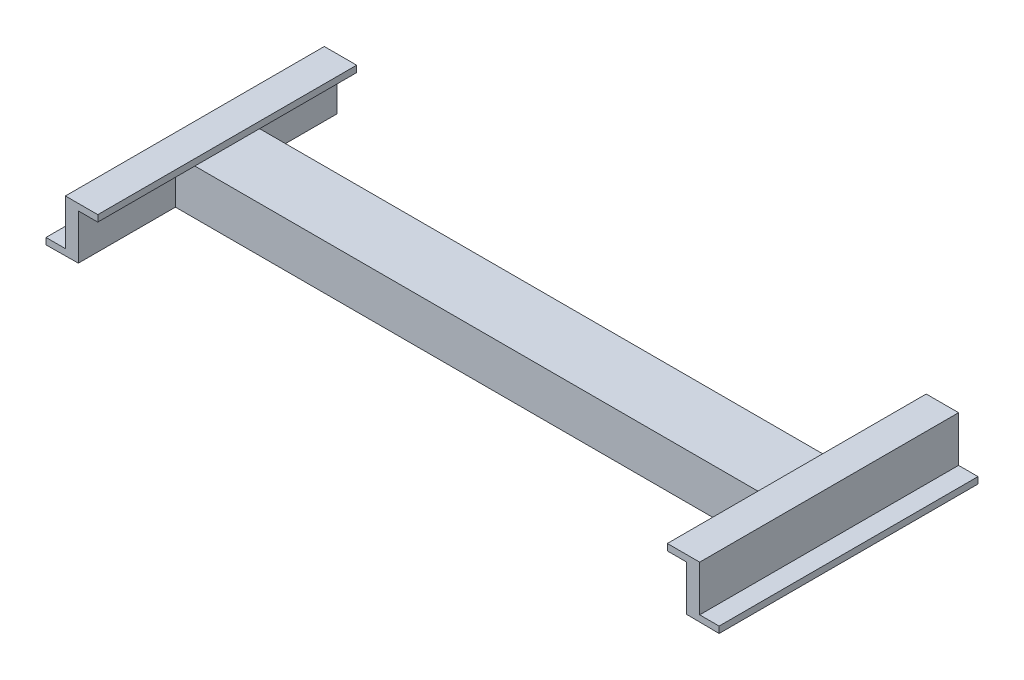
SolidWorks part; units mm, degrees
ref_plane "Front Plane" through (0, 0, 0) normal (0, 0, 1) x (1, 0, 0)
ref_plane "Top Plane" through (0, 0, 0) normal (0, 1, 0) x (1, 0, 0)
ref_plane "Right Plane" through (0, 0, 0) normal (1, 0, 0) x (0, 0, -1)
sketch "Sketch1" plane through (0, 0, 0) normal (0, 0, 1) x (1, 0, 0)
  line L0 (-59.8882, 0) -> (68.2642, 0) construction
  line L1 (0, 47.0101) -> (0, -48.8947) construction
  line L3 (10.5867, 38.0433) -> (10.5867, -32.4739)
  line L4 (10.5867, -32.4739) -> (40.5867, -32.4739)
  line L5 (40.5867, -32.4739) -> (40.5867, -42.4739)
  line L6 (40.5867, -42.4739) -> (-9.4133, -41.9567)
  line L7 (-9.4133, -41.9567) -> (-9.4133, 28.0433)
  line L8 (-9.4133, 28.0433) -> (-39.4133, 28.0433)
  line L9 (-39.4133, 28.0433) -> (-39.4133, 38.0433)
  line L11 (-39.4133, 38.0433) -> (10.5867, 38.0433)
  dimension "D1" = 10
  dimension "D2" = 50
  dimension "D3" = 70
  dimension "D4" = 30
  dimension "D5" = 30
  dimension "D6" = 10
extrude "Boss-Extrude1" add sketch "Sketch1" along normal blind 400
sketch "Sketch2" plane through (-9.4133, 0, 0) normal (-1, 0, 0) x (0, 0, 1)
  line L0 (0, 28.0433) -> (0, -41.9567) construction
  line L1 (150, 28.0433) -> (250, 28.0433)
  line L2 (150, 28.0433) -> (150, -41.9567)
  line L4 (250, 28.0433) -> (250, -41.9567)
  line L5 (400, 28.0433) -> (400, -41.9567) construction
  line L6 (160, 18.0433) -> (240, 18.0433)
  line L7 (150, -41.9567) -> (160, -41.9567)
  line L8 (400, -41.9567) -> (0, -41.9567) construction
  line L9 (160, -41.9567) -> (160, 18.0433)
  line L11 (240, 18.0433) -> (240, -41.9567)
  line L12 (240, -41.9567) -> (250, -41.9567)
  point P6 (150, -6.9567)
  dimension "D1" = 150
  dimension "D2" = 150
  dimension "D3" = 10
  dimension "D4" = 10
extrude "Boss-Extrude2" add sketch "Sketch2" along normal blind 470
ref_plane "Plane1" through (-479.4133, 0, 0) normal (-1, 0, 0) x (0, 0, 1)
mirror "Mirror2" about plane through (-479.4133, 0, 0) normal (-1, 0, 0) of "Boss-Extrude2", "Boss-Extrude1"
mirror "Mirror3" about plane through (-479.4133, 0, 0) normal (-1, 0, 0) of "Boss-Extrude1"
